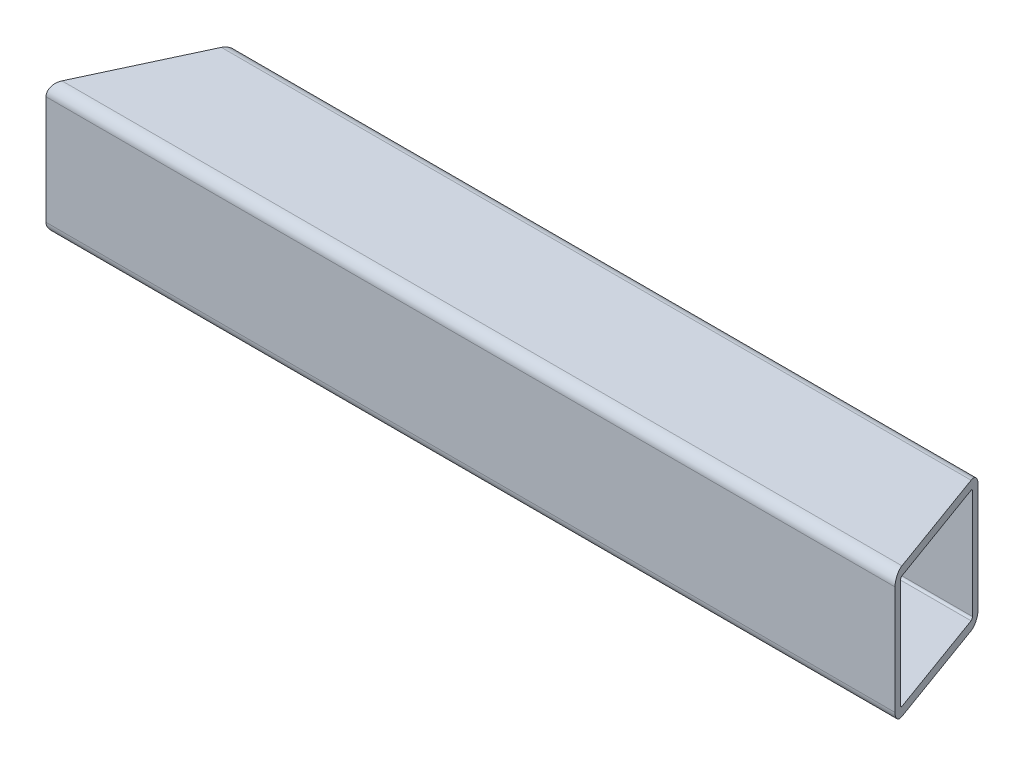
SolidWorks part; units mm, degrees
ref_plane "Front Plane" through (0, 0, 0) normal (0, 0, 1) x (1, 0, 0)
ref_plane "Top Plane" through (0, 0, 0) normal (0, 1, 0) x (1, 0, 0)
ref_plane "Right Plane" through (0, 0, 0) normal (1, 0, 0) x (0, 0, -1)
sketch "Sketch1" plane through (0, 0, 0) normal (1, 0, 0) x (0, 0, -1)
  line L1 (-15.875, 19.05) -> (15.875, 19.05)
  line L2 (-19.05, 15.875) -> (-19.05, -15.875)
  line L3 (-15.875, -19.05) -> (15.875, -19.05)
  line L4 (19.05, 15.875) -> (19.05, -15.875)
  line L5 (-19.05, 19.05) -> (19.05, -19.05) construction
  line L6 (-19.05, -19.05) -> (19.05, 19.05) construction
  arc A0 (-19.05, -15.875) -> (-15.875, -19.05) centre (-15.875, -15.875) ccw
  arc A1 (15.875, -19.05) -> (19.05, -15.875) centre (15.875, -15.875) ccw
  arc A2 (19.05, 15.875) -> (15.875, 19.05) centre (15.875, 15.875) ccw
  arc A3 (-15.875, 19.05) -> (-19.05, 15.875) centre (-15.875, 15.875) ccw
  point P0 (0, 0)
  dimension "D3" = 3.175
  dimension "D1" = 38.1
  dimension "D2" = 38.1
extrude "Extrude-Thin1" add sketch "Sketch1" along normal mid plane 247.9751 thin
sketch "Sketch2" plane through (0, -19.05, 0) normal (0, -1, 0) x (1, 0, 0)
  line L0 (123.9876, 0) -> (-123.9876, 0) construction
  line L1 (123.9876, 15.875) -> (123.9876, -15.875) construction
  line L2 (-123.9876, 15.875) -> (-123.9876, -15.875) construction
  line L3 (73.1876, 15.875) -> (73.1876, -15.875) construction
  line L4 (123.9876, 15.875) -> (-123.9876, 15.875) construction
  line L5 (123.9876, -15.875) -> (-123.9876, -15.875) construction
  line L6 (-85.5624, 15.875) -> (-85.5624, -15.875) construction
  dimension "D1" = 209.55
  dimension "D2" = 50.8
sketch "Sketch3" plane through (0, 19.05, 0) normal (0, 1, 0) x (1, 0, 0)
  line L0 (123.9876, -19.05) -> (110.1203, 19.05)
  line L1 (123.9876, 19.05) -> (-123.9876, 19.05) construction
  line L3 (123.9876, 15.875) -> (123.9876, -15.875) construction
  dimension "D1" = 20
extrude "Cut-Extrude1" cut sketch "Sketch3" against normal through all and the other way through all flip side to cut
sketch "Sketch4" plane through (0, 19.05, 0) normal (0, 1, 0) x (1, 0, 0)
  line L0 (-123.9876, -19.05) -> (-106.2212, 19.05)
  line L1 (110.1203, 19.05) -> (-123.9876, 19.05) construction
  line L2 (-123.9876, 15.875) -> (-123.9876, -15.875) construction
  dimension "D1" = 25
extrude "Cut-Extrude2" cut sketch "Sketch4" against normal through all and the other way through all
